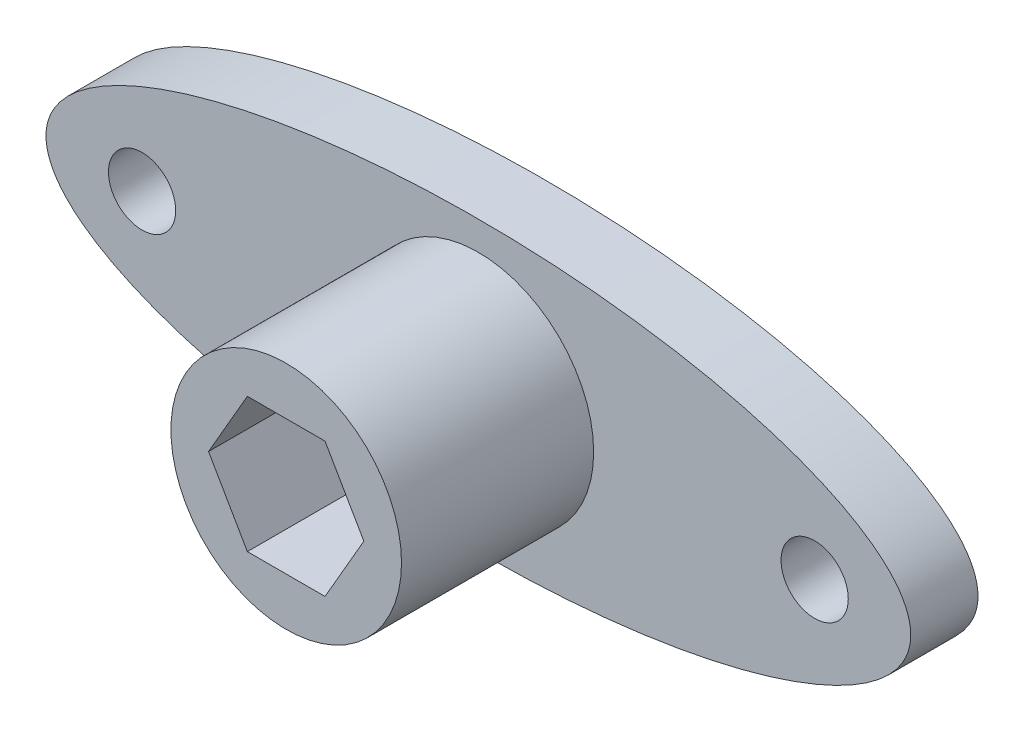
SolidWorks part; units mm, degrees
material "Plain Carbon Steel"
ref_plane "Front Plane" through (0, 0, 0) normal (0, 0, 1) x (1, 0, 0)
ref_plane "Top Plane" through (0, 0, 0) normal (0, 1, 0) x (1, 0, 0)
ref_plane "Right Plane" through (0, 0, 0) normal (1, 0, 0) x (0, 0, -1)
sketch "Sketch1" plane through (0, 0, 0) normal (0, 0, 1) x (1, 0, 0)
  circle A0 centre (-17.5, 0) radius 1.75
  circle A1 centre (17.5, 0) radius 1.75
  ellipse E0 centre (0, 0) end of major axis (22.5, 0) minor radius 7.5
  dimension "D3" = 3.5
  dimension "D4" = 3.5
  dimension "D1" = 45
  dimension "D2" = 15
  dimension "D5" = 5
  dimension "D6" = 5
extrude "Boss-Extrude2" add sketch "Sketch1" along normal blind 3.5
sketch "Sketch3" plane through (0, 0, 3.5) normal (0, 0, 1) x (1, 0, 0)
  circle A0 centre (0, 0) radius 6
  ellipse E0 centre (0, 0) end of major axis (22.5, 0) minor radius 7.5 construction
  ellipse E1 centre (0, 0) end of major axis (22.5, 0) minor radius 7.5
  dimension "D1" = 12
extrude "Boss-Extrude3" add sketch "Sketch3" along normal blind 10 contours A0
sketch "Sketch4" plane through (0, 0, 13.5) normal (0, 0, 1) x (1, 0, 0)
  line L1 (4.0415, 0) -> (2.0207, 3.5)
  line L2 (2.0207, 3.5) -> (-2.0207, 3.5)
  line L3 (-2.0207, 3.5) -> (-4.0415, 0)
  line L4 (-4.0415, 0) -> (-2.0207, -3.5)
  line L5 (-2.0207, -3.5) -> (2.0207, -3.5)
  line L6 (2.0207, -3.5) -> (4.0415, 0)
  circle A0 centre (0, 0) radius 3.5 construction
  dimension "D1" = 7
extrude "Cut-Extrude5" cut sketch "Sketch4" against normal offset from surface (7 mm away) 3 up to face at (6, 0, 3.5)
